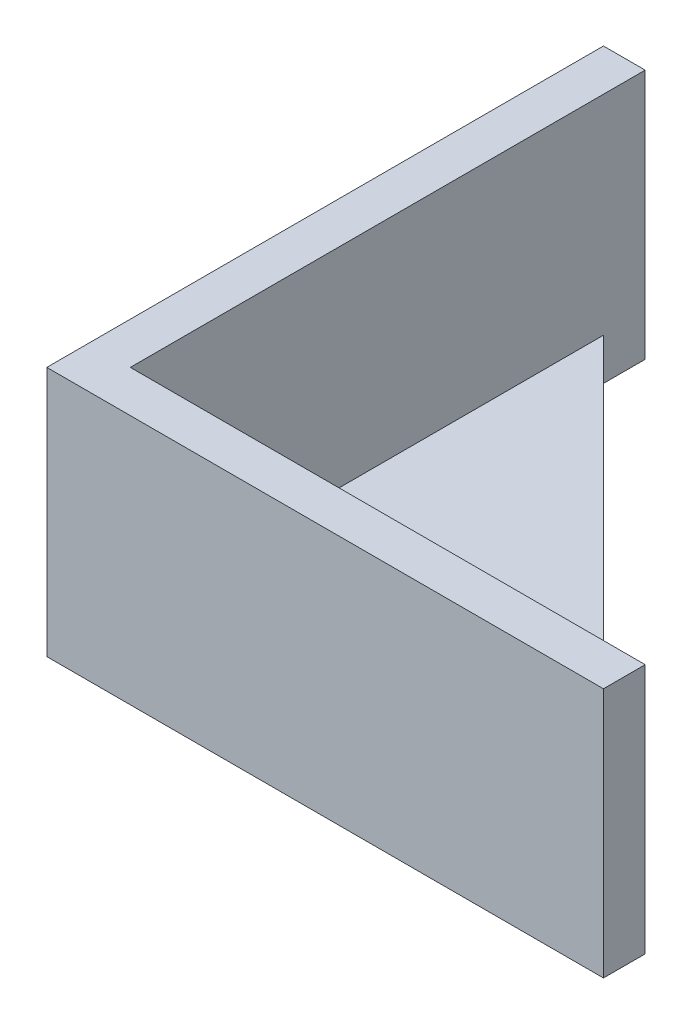
SolidWorks part; units mm, degrees
ref_plane "前视基准面" through (0, 0, 0) normal (0, 0, 1) x (1, 0, 0)
ref_plane "上视基准面" through (0, 0, 0) normal (0, 1, 0) x (1, 0, 0)
ref_plane "右视基准面" through (0, 0, 0) normal (1, 0, 0) x (0, 0, -1)
other "Configuration Table"
sketch "草图1" plane through (0, 0, 0) normal (0, 1, 0) x (1, 0, 0)
  line L0 (0, 0) -> (0, 40)
  line L1 (0, 0) -> (40, 0)
  line L2 (0, 40) -> (40, 0)
  line L3 (0, 40) -> (3, 40)
  line L4 (3, 40) -> (3, 37)
  line L5 (40, 0) -> (40, 3)
  line L6 (40, 3) -> (37, 3)
  dimension "D1" = 40
  dimension "D2" = 3
  dimension "D3" = 3
extrude "凸台-拉伸1" add sketch "草图1" along normal blind 3 contours L4 L3 L2 | L2 L0 L1 | L5 L6 L2
sketch "草图2" plane through (0, 3, 0) normal (0, 1, 0) x (1, 0, 0)
  line L0 (3, 37) -> (37, 3)
  line L2 (37, 3) -> (40, 3)
  line L4 (40, 3) -> (40, 0)
  line L6 (3, 37) -> (3, 0)
  line L7 (0, 3) -> (37, 3)
  line L9 (3, 37) -> (37, 3)
  line L10 (37, 3) -> (40, 3)
  line L11 (40, 3) -> (40, 0)
  line L12 (40, 0) -> (0, 0)
  line L13 (0, 0) -> (0, 40)
  line L14 (0, 40) -> (3, 40)
  line L15 (3, 40) -> (3, 37)
  line L16 (40, 0) -> (0, 0)
  line L17 (0, 0) -> (0, 40)
  line L18 (0, 40) -> (3, 40)
  line L19 (3, 40) -> (3, 37)
  line L20 (0, 0) -> (0, 40) construction
  point P6 (9.1061, 3)
  point P7 (37, 3)
  point P11 (0, 0)
  point P12 (38.6471, 3)
  point P13 (0, 3)
extrude "凸台-拉伸2" add sketch "草图2" along normal blind 15
